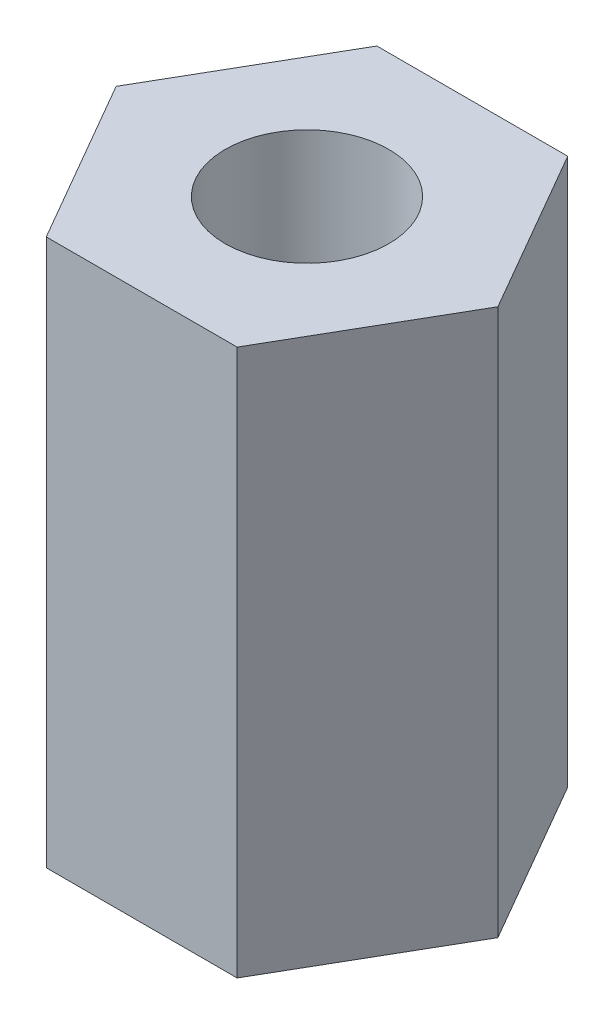
SolidWorks part; units mm, degrees
material "Alum Plate"
ref_plane "Front Plane" through (0, 0, 0) normal (0, 0, 1) x (1, 0, 0)
ref_plane "Top Plane" through (0, 0, 0) normal (0, 1, 0) x (1, 0, 0)
ref_plane "Right Plane" through (0, 0, 0) normal (1, 0, 0) x (0, 0, -1)
other "Bounding Box"
ref_plane "Default Plane" through (13.8565, 3.175, 6.7999) normal (0, -1, 0) x (-1, 0, 0)
sketch "Sketch1" plane through (0, 0, 0) normal (0, 1, 0) x (1, 0, 0)
  line L1 (6.9657, 0) -> (3.4829, 6.0325)
  line L2 (3.4829, 6.0325) -> (-3.4829, 6.0325)
  line L3 (-3.4829, 6.0325) -> (-6.9657, 0)
  line L4 (-6.9657, 0) -> (-3.4829, -6.0325)
  line L5 (-3.4829, -6.0325) -> (3.4829, -6.0325)
  line L6 (3.4829, -6.0325) -> (6.9657, 0)
  circle A0 centre (0, 0) radius 6.0325 construction
  circle A1 centre (0, 0) radius 2.9845
  dimension "D2" = 5.969
  dimension "D1" = 12.065
extrude "Boss-Extrude1" add sketch "Sketch1" along normal mid plane 19.939
